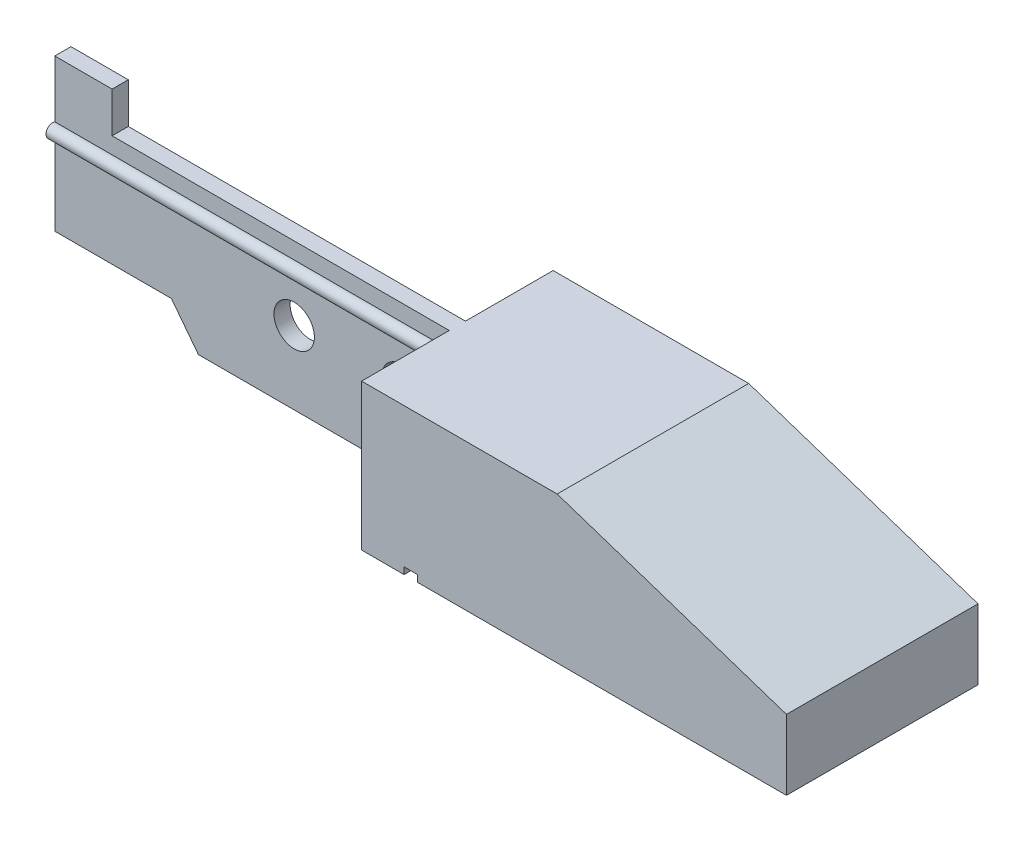
SolidWorks part; units mm, degrees
material "PF"
ref_plane "Płaszczyzna przednia" through (0, 0, 0) normal (0, 0, 1) x (1, 0, 0)
ref_plane "Płaszczyzna górna" through (0, 0, 0) normal (0, 1, 0) x (1, 0, 0)
ref_plane "Płaszczyzna prawa" through (0, 0, 0) normal (1, 0, 0) x (0, 0, -1)
sketch "Szkic1" plane through (0, 0, 0) normal (0, 0, 1) x (1, 0, 0)
  line L0 (-36.8787, 9.2137) -> (-5.3787, 9.2137)
  line L1 (-5.3787, 9.2137) -> (-5.3787, 14.4138)
  line L2 (-36.8787, 9.2137) -> (-36.8787, 20.0637)
  line L3 (-36.8787, 20.0637) -> (-22.3787, 20.0637)
  line L4 (-22.3787, 20.0637) -> (-5.3787, 14.4138)
  dimension "D1" = 31.5
  dimension "D2" = 10.85
  dimension "D3" = 14.5
  dimension "D4" = 5.2
  dimension "D5" = 17.9143
extrude "Dodanie-wyciągnięcie1" add sketch "Szkic1" along normal blind 14.2
sketch "Szkic2" plane through (-36.8787, 0, 0) normal (-1, 0, 0) x (0, 0, 1)
  line L0 (6.5, 20.0637) -> (6.5, 9.2137)
  line L2 (7.7, 20.0637) -> (7.7, 9.2137)
  line L4 (6.5, 9.2137) -> (7.7, 9.2137)
  line L6 (7.7, 20.0637) -> (6.5, 20.0637)
extrude "Dodanie-wyciągnięcie3" add sketch "Szkic2" along normal blind 29.25
sketch "Szkic6" plane through (0, 20.0637, 0) normal (0, 1, 0) x (1, 0, 0)
  line L0 (-61.8772, -7.7) -> (-61.8772, -6.5)
  line L3 (-66.1287, -6.5) -> (-66.1287, -7.7)
  line L4 (-61.8772, -6.5) -> (-66.1287, -6.5)
  line L5 (-61.8772, -7.7) -> (-66.1287, -7.7)
extrude "Dodanie-wyciągnięcie4" add sketch "Szkic6" along normal blind 3
sketch "Szkic20" plane through (0, 0, 7.7) normal (0, 0, 1) x (1, 0, 0)
  circle A0 centre (-40.3787, 14.6337) radius 1.5
extrude "Wytnij-wyciągnięcie5" cut sketch "Szkic20" against normal blind 10
sketch "Szkic10" plane through (0, 9.2137, 0) normal (0, -1, 0) x (1, 0, 0)
  line L2 (-33.7292, 6.3694) -> (-33.7292, 14.2)
  line L3 (-36.8787, 14.2) -> (-5.3787, 14.2) construction
  line L4 (-33.7292, 14.2) -> (-32.7292, 14.2)
  line L5 (-32.7292, 14.2) -> (-32.7292, 0)
  line L6 (-36.8787, 0) -> (-5.3787, 0) construction
  line L7 (-32.7292, 0) -> (-33.7292, 0)
  line L8 (-33.7292, 0) -> (-33.7292, 6.3694)
  dimension "D1" = 14.2
  dimension "D2" = 7.8306
  dimension "D3" = 6.3694
extrude "Wytnij-wyciągnięcie3" cut sketch "Szkic10" against normal blind 0.5
sketch "Szkic11" plane through (-36.8787, 0, 0) normal (-1, 0, 0) x (0, 0, 1)
  circle A2 centre (7.85, 18.3637) radius 0.5
  dimension "D1" = 1
extrude "Dodanie-wyciągnięcie5" add sketch "Szkic11" along normal up to surface (29.25 mm away) contours A2
sketch "Szkic21" plane through (0, 0, 6.5) normal (0, 0, -1) x (-1, 0, 0)
  line L0 (55.4787, 9.2137) -> (66.1287, 9.2137)
  line L1 (66.1287, 9.2137) -> (36.8787, 9.2137) construction
  line L2 (66.1287, 9.2137) -> (66.1287, 11.8137)
  line L3 (66.1287, 23.0637) -> (66.1287, 9.2137) construction
  line L4 (66.1287, 11.8137) -> (57.4787, 11.8137)
  line L5 (57.4787, 11.8137) -> (55.4787, 9.2137)
extrude "Wytnij-wyciągnięcie6" cut sketch "Szkic21" against normal blind 10
sketch "Szkic23" plane through (0, 0, 6.5) normal (0, 0, -1) x (-1, 0, 0)
  circle A0 centre (48.3787, 14.6338) radius 1.5
extrude "Wytnij-wyciągnięcie8" cut sketch "Szkic23" against normal blind 10
ref_plane "Oś symetrii przycisku" through (0, 0, 7.1) normal (0, 0, 1) x (1, 0, 0)
